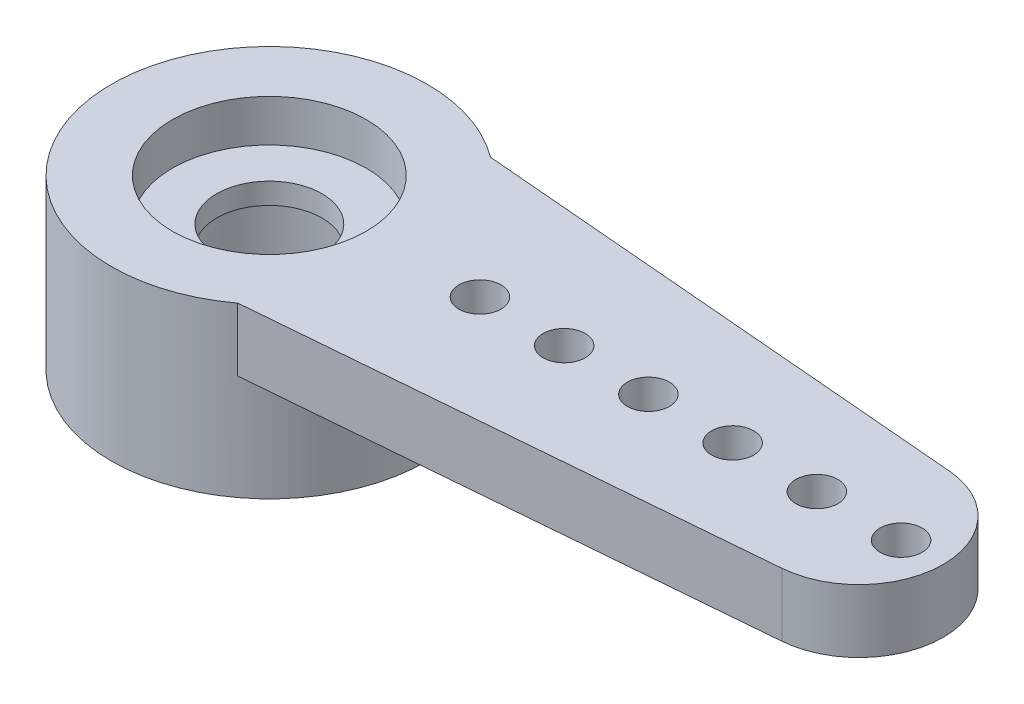
SolidWorks part; units mm, degrees
ref_plane "Front Plane" through (0, 0, 0) normal (0, 0, 1) x (1, 0, 0)
ref_plane "Top Plane" through (0, 0, 0) normal (0, 1, 0) x (1, 0, 0)
ref_plane "Right Plane" through (0, 0, 0) normal (1, 0, 0) x (0, 0, -1)
sketch "Sketch1" plane through (0, 0, 0) normal (0, 1, 0) x (1, 0, 0)
  circle A0 centre (0, 0) radius 3.75
  dimension "D1" = 7.5
extrude "Boss-Extrude1" add sketch "Sketch1" along normal blind 4
sketch "Sketch2" plane through (0, 4, 0) normal (0, 1, 0) x (1, 0, 0)
  circle A0 centre (0, 0) radius 2.3
  dimension "D1" = 4.6
extrude "Cut-Extrude1" cut sketch "Sketch2" against normal blind 1
sketch "Sketch3" plane through (0, 4, 0) normal (0, 1, 0) x (1, 0, 0)
  line L3 (0, -3.75) -> (0, 3.75) construction
  line L4 (14.1684, -1.9929) -> (2.25, -3)
  line L5 (14.1684, 1.9929) -> (2.25, 3)
  circle A1 centre (0, 0) radius 3.75 construction
  arc A3 (2.25, 3) -> (2.25, -3) centre (0, 0) cw
  arc A4 (14.1684, 1.9929) -> (14.1684, -1.9929) centre (14, 0) cw
  circle A11 centre (15, 0) radius 0.5
  circle A12 centre (5, 0) radius 0.5
  circle A13 centre (7, 0) radius 0.5
  circle A14 centre (9, 0) radius 0.5
  circle A15 centre (11, 0) radius 0.5
  circle A16 centre (13, 0) radius 0.5
  point P4 (0, 0)
extrude "Boss-Extrude2" add sketch "Sketch3" against normal blind 1.5
sketch "Sketch4" plane through (0, 3, 0) normal (0, 1, 0) x (1, 0, 0)
  circle A0 centre (0, 0) radius 1.25
  dimension "D1" = 2.5
extrude "Cut-Extrude2" cut sketch "Sketch4" against normal blind 4.5
sketch "Sketch5" plane through (0, 0, 0) normal (0, -1, 0) x (1, 0, 0)
  circle A0 centre (0, 0) radius 2.3
  dimension "D1" = 4.6
extrude "Cut-Extrude3" cut sketch "Sketch5" against normal blind 2.5
